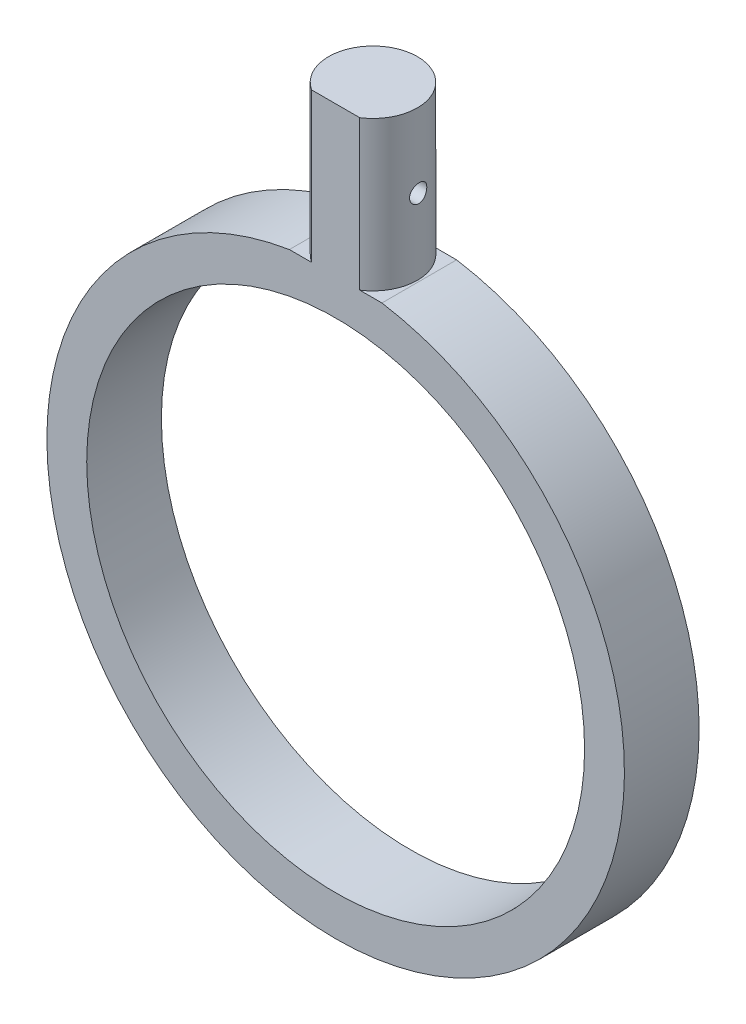
SolidWorks part; units mm, degrees
ref_plane "Front Plane" through (0, 0, 0) normal (0, 0, 1) x (1, 0, 0)
ref_plane "Top Plane" through (0, 0, 0) normal (0, 1, 0) x (1, 0, 0)
ref_plane "Right Plane" through (0, 0, 0) normal (1, 0, 0) x (0, 0, -1)
sketch "Sketch1" plane through (0, 0, 0) normal (0, 0, 1) x (1, 0, 0)
  line L0 (-5.9006, 36.3543) -> (5.9006, 36.3543)
  circle A0 centre (0, 0) radius 31.75
  arc A1 (-5.9006, 36.3543) -> (5.9006, 36.3543) centre (0, 0) ccw
  circle A2 centre (0, 0) radius 36.83 construction
  dimension "D2" = 63.5
  dimension "D1" = 5.08
extrude "Boss-Extrude1" add sketch "Sketch1" along normal blind 9.525
sketch "Sketch2" plane through (0, 36.3543, 0) normal (0, 1, 0) x (1, 0, 0)
  line L0 (-3.0677, -9.525) -> (3.0677, -9.525)
  arc A0 (3.0677, -9.525) -> (-3.0677, -9.525) centre (0, -4.7625) ccw
extrude "Boss-Extrude2" add sketch "Sketch2" along normal blind 19.05
ref_plane "Plane1" through (5.9006, 0, 0) normal (1, 0, 0) x (0, 0, -1)
sketch "Sketch3" plane through (5.9006, 0, 0) normal (1, 0, 0) x (0, 0, -1)
  line L0 (-4.7825, 36.3543) -> (-4.3112, 55.4043) construction
  line L2 (0.9025, 55.4043) -> (-9.525, 55.4043) construction
  line L3 (-10.4275, 45.8793) -> (0.9025, 45.8793) construction
  line L4 (0.9025, 36.3543) -> (0.9025, 55.4043) construction
  line L5 (0.9025, 36.3543) -> (0.9025, 55.4043) construction
  line L6 (-9.525, 36.3543) -> (0, 36.3543) construction
  line L7 (-9.525, 36.3543) -> (0, 36.3543) construction
  circle A0 centre (-4.5469, 45.8793) radius 1.143
  dimension "D1" = 2.286
extrude "Cut-Extrude1" cut sketch "Sketch3" against normal through all
sketch "Sketch4" plane through (0, 55.4043, 0) normal (0, 1, 0) x (1, 0, 0)
  line L1 (-6.0436, -9.6398) -> (5.5236, -9.6398)
  line L2 (-6.0436, -9.6398) -> (-6.0436, -13.5762)
  line L3 (-6.0436, -13.5762) -> (5.5236, -13.5762)
  line L4 (5.5236, -9.6398) -> (5.5236, -13.5762)
extrude "Cut-Extrude2" cut sketch "Sketch4" against normal through all
